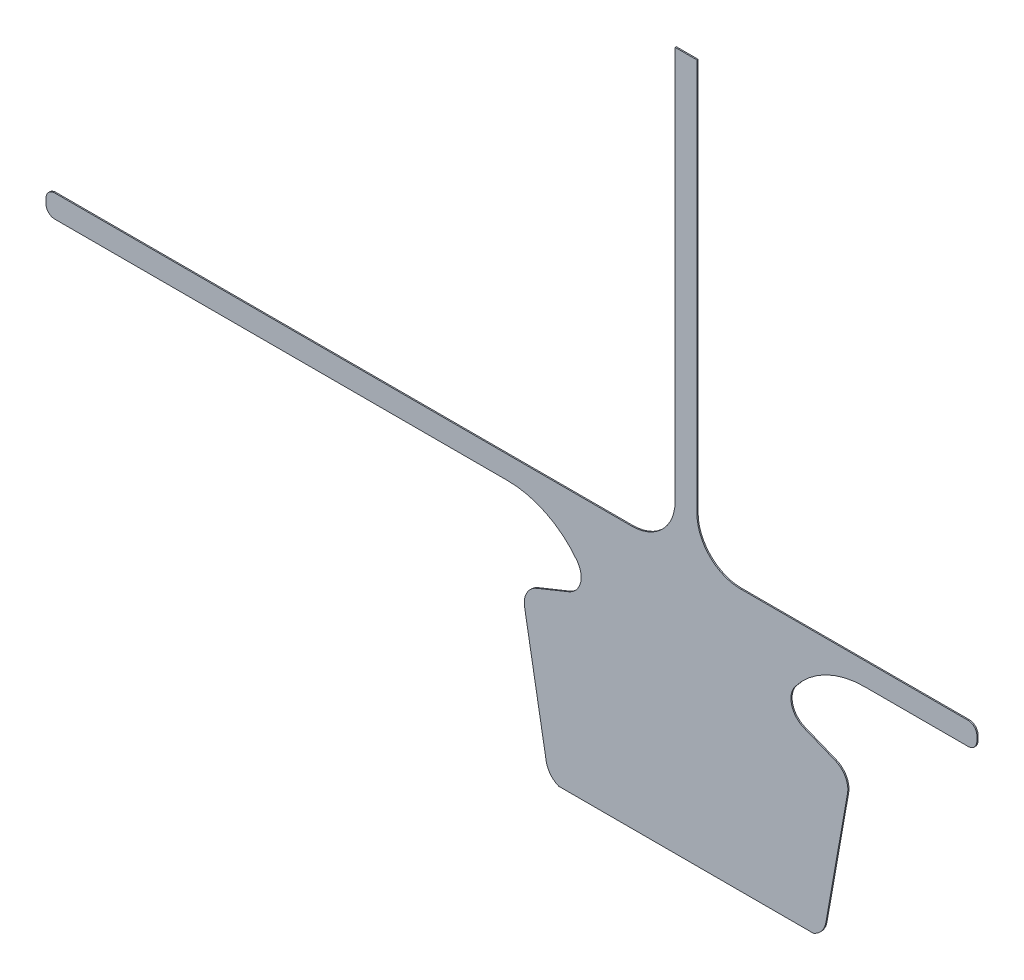
SolidWorks part; units mm, degrees
ref_plane "Front Plane" through (0, 0, 0) normal (0, 0, 1) x (1, 0, 0)
ref_plane "Top Plane" through (0, 0, 0) normal (0, 1, 0) x (1, 0, 0)
ref_plane "Right Plane" through (0, 0, 0) normal (1, 0, 0) x (0, 0, -1)
sketch "Sketch1" plane through (0, 0, 0) normal (0, 0, 1) x (1, 0, 0)
  line L14 (-102.6905, 151.3184) -> (-130.1387, 140.2286)
  line L15 (-551.2654, 208.8297) -> (-155.9953, 208.8297)
  line L16 (-558.8854, 220.98) -> (-558.8854, 216.4497)
  line L17 (-47.442, 228.6) -> (-551.2654, 228.6)
  line L18 (-9.525, 609.6) -> (-9.525, 266.517)
  line L19 (9.525, 609.6) -> (-9.525, 609.6)
  line L20 (9.525, 266.517) -> (9.525, 609.6)
  line L21 (246.2946, 228.6) -> (47.442, 228.6)
  line L22 (253.9146, 216.4497) -> (253.9146, 220.98)
  line L23 (155.9953, 208.8297) -> (246.2946, 208.8297)
  line L24 (130.1387, 140.2286) -> (102.6905, 151.3184)
  line L25 (122.083, 13.4403) -> (140.988, 120.6558)
  line L26 (-111.1277, 0) -> (111.1277, 0)
  line L27 (-140.988, 120.6558) -> (-122.083, 13.4403)
  line L28 (0, 609.6) -> (0, -115.4044) construction
  line L29 (-340.5682, 0) -> (340.5682, 0) construction
  arc A14 (-102.6905, 151.3184) -> (-95.1549, 178.5089) centre (-109.351, 167.8037) ccw
  arc A15 (-95.1549, 178.5089) -> (-155.9953, 208.8297) centre (-155.9953, 132.6297) ccw
  arc A16 (-558.8854, 216.4497) -> (-551.2654, 208.8297) centre (-551.2654, 216.4497) ccw
  arc A17 (-551.2654, 228.6) -> (-558.8854, 220.98) centre (-551.2654, 220.98) ccw
  arc A18 (-47.442, 228.6) -> (-9.525, 266.517) centre (-47.442, 266.517) ccw
  arc A19 (9.525, 266.517) -> (47.442, 228.6) centre (47.442, 266.517) ccw
  arc A20 (253.9146, 220.98) -> (246.2946, 228.6) centre (246.2946, 220.98) ccw
  arc A21 (246.2946, 208.8297) -> (253.9146, 216.4497) centre (246.2946, 216.4497) ccw
  arc A22 (155.9953, 208.8297) -> (95.1549, 178.5089) centre (155.9953, 132.6297) ccw
  arc A23 (95.1549, 178.5089) -> (102.6905, 151.3184) centre (109.351, 167.8037) ccw
  arc A24 (140.988, 120.6558) -> (130.1387, 140.2286) centre (123.4782, 123.7433) ccw
  arc A25 (111.1277, 0) -> (122.083, 13.4403) centre (104.5732, 16.5277) ccw
  arc A26 (-122.083, 13.4403) -> (-111.1277, 0) centre (-104.5732, 16.5277) ccw
  arc A27 (-130.1387, 140.2286) -> (-140.988, 120.6558) centre (-123.4782, 123.7433) ccw
  point P46 (0, 0)
  dimension "D1" = 17.78
  dimension "D2" = 76.2
  dimension "D3" = 7.62
  dimension "D4" = 37.917
  dimension "D5" = 9.525
  dimension "D6" = 95.1549
  dimension "D7" = 102.6905
  dimension "D8" = 104.5732
  dimension "D9" = 109.351
  dimension "D10" = 111.1277
  dimension "D11" = 122.083
  dimension "D12" = 123.4782
  dimension "D13" = 228.6
  dimension "D14" = 609.6
  dimension "D16" = 253.9146
  dimension "D28" = 558.8854
extrude "Boss-Extrude1" add sketch "Sketch1" along normal blind 1.016
